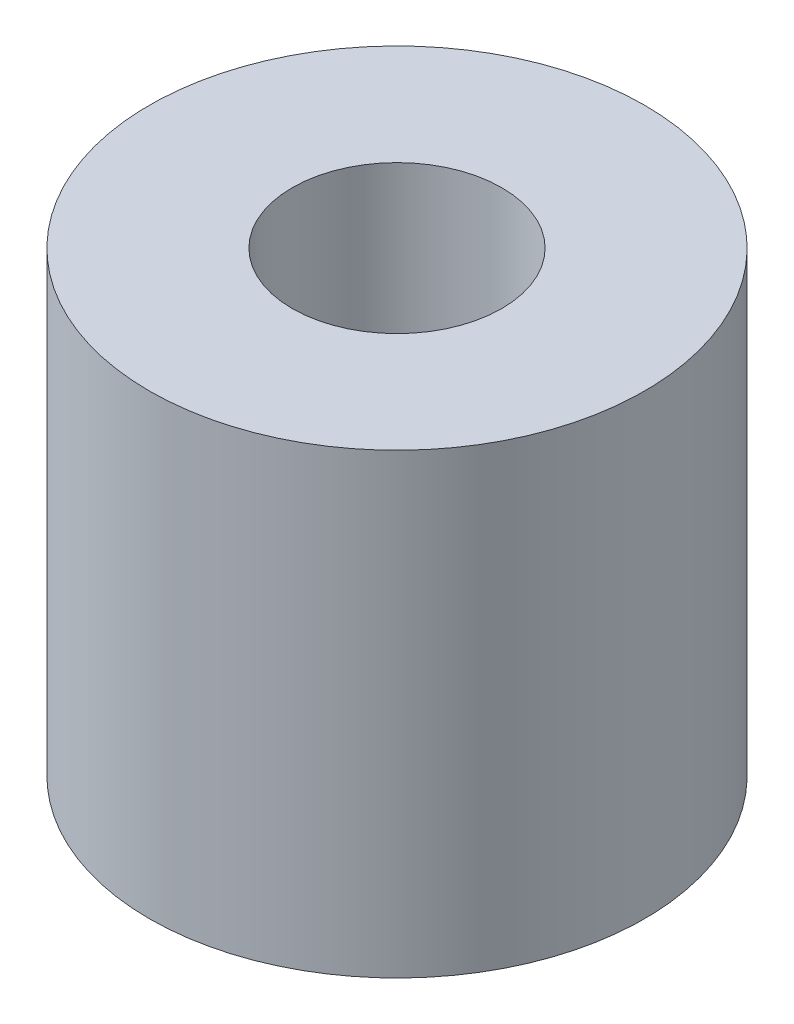
SolidWorks part; units mm, degrees
ref_plane "Front Plane" through (0, 0, 0) normal (0, 0, 1) x (1, 0, 0)
ref_plane "Top Plane" through (0, 0, 0) normal (0, 1, 0) x (1, 0, 0)
ref_plane "Right Plane" through (0, 0, 0) normal (1, 0, 0) x (0, 0, -1)
sketch "Sketch1" plane through (0, 0, 0) normal (0, 1, 0) x (1, 0, 0)
  circle A0 centre (0, 0) radius 1.65
  circle A1 centre (0, 0) radius 3.9
extrude "Boss-Extrude1" add sketch "Sketch1" along normal blind 7.2
